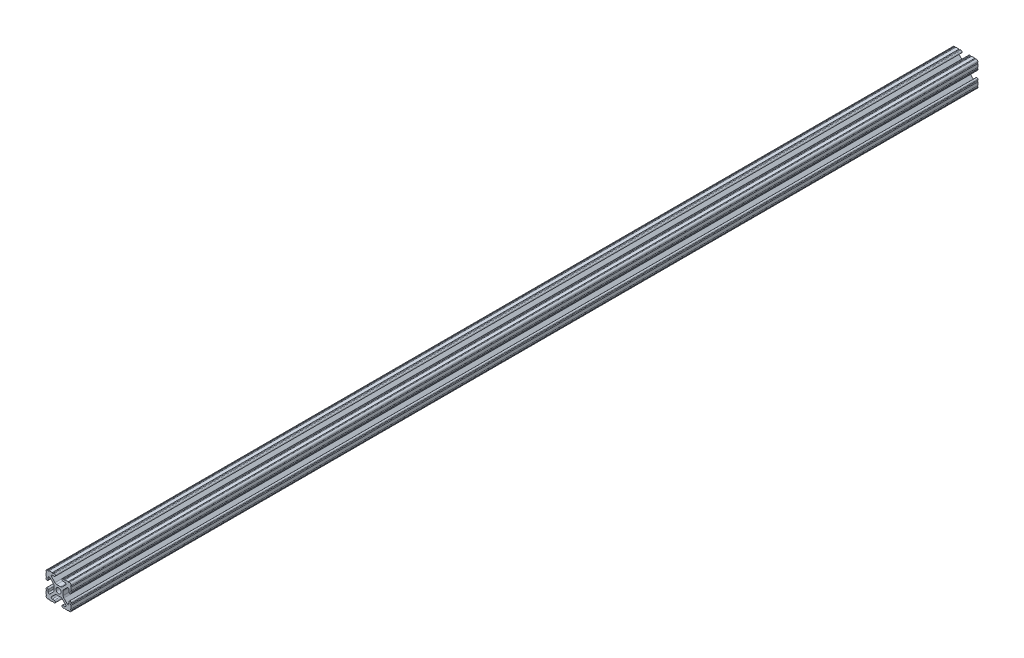
SolidWorks part; units mm, degrees
ref_plane "Front Plane" through (0, 0, 0) normal (0, 0, 1) x (1, 0, 0)
ref_plane "Top Plane" through (0, 0, 0) normal (0, 1, 0) x (1, 0, 0)
ref_plane "Right Plane" through (0, 0, 0) normal (1, 0, 0) x (0, 0, -1)
sketch "Sketch1" plane through (0, 0, 0) normal (0, 0, 1) x (1, 0, 0)
  line L0 (0, -12.7) -> (0, 12.7) construction
  line L1 (12.7, 0) -> (-12.7, 0) construction
  line L2 (3.2512, 12.7) -> (-3.2512, 12.7) construction
  line L3 (0, -4.5212) -> (0, 4.5212) construction
  line L4 (-3.2512, 12.7) -> (-3.2512, 10.4902) construction
  line L5 (12.7, -7.4168) -> (12.7, 7.4168) construction
  line L6 (0, -2.6035) -> (0, 2.6035) construction
  point P4 (0, 0)
  point P8 (0, 0)
  point P11 (0, 12.7)
  point P14 (0, 0)
  point P18 (12.7, 0)
  point P21 (0, 0)
sketch "Sketch2" plane through (0, 0, 0) normal (1, 0, 0) x (0, 0, -1)
  line L0 (-457.2, 0) -> (457.2, 0) construction
  point P4 (0, 0)
  dimension "Length" = 914.4
sketch "Sketch3" plane through (0, 0, 0) normal (0, 0, 1) x (1, 0, 0)
  line L1 (12.7, -12.7) -> (-12.7, -12.7)
  line L2 (12.7, -12.7) -> (12.7, 12.7)
  line L3 (12.7, 12.7) -> (-12.7, 12.7)
  line L4 (-12.7, -12.7) -> (-12.7, 12.7)
  line L5 (12.7, -12.7) -> (-12.7, 12.7) construction
  line L6 (12.7, 12.7) -> (-12.7, -12.7) construction
  point P0 (0, 0)
extrude "Boss-Extrude1" add sketch "Sketch3" along normal up to vertex (457.2 mm away) and the other way up to vertex (457.2 mm away) up to point (0, 0, 457.2) other way up to point (0, 0, -457.2)
sketch "Sketch4" plane through (0, 0, 457.2) normal (0, 0, 1) x (1, 0, 0)
  line L0 (-3.2512, 12.7) -> (-3.2512, 10.4902)
  line L1 (-3.2512, 10.4902) -> (-8.9276, 10.4902)
  line L2 (-8.9276, 10.4902) -> (-2.9586, 4.5212)
  line L3 (-2.9586, 4.5212) -> (2.9586, 4.5212)
  line L4 (0, -12.7) -> (0, 12.7) construction
  line L5 (12.7, 12.7) -> (-12.7, 12.7) construction
  line L6 (0, 12.7) -> (0, -12.7) construction
  line L7 (-12.7, 0) -> (12.7, 0) construction
  line L8 (-12.7, 12.7) -> (0, 0) construction
  line L9 (-12.7, 3.2512) -> (-10.4902, 3.2512)
  line L10 (-10.4902, 3.2512) -> (-10.4902, 8.9276)
  line L11 (-10.4902, 8.9276) -> (-4.5212, 2.9586)
  line L12 (-4.5212, 2.9586) -> (-4.5212, -2.9586)
  line L13 (4.5212, 2.9586) -> (4.5212, -2.9586)
  line L14 (10.4902, 8.9276) -> (4.5212, 2.9586)
  line L15 (10.4902, 3.2512) -> (10.4902, 8.9276)
  line L16 (12.7, 3.2512) -> (10.4902, 3.2512)
  line L17 (8.9276, 10.4902) -> (2.9586, 4.5212)
  line L18 (3.2512, 10.4902) -> (8.9276, 10.4902)
  line L19 (3.2512, 12.7) -> (3.2512, 10.4902)
  line L20 (3.2512, -12.7) -> (3.2512, -10.4902)
  line L21 (3.2512, -10.4902) -> (8.9276, -10.4902)
  line L22 (8.9276, -10.4902) -> (2.9586, -4.5212)
  line L23 (12.7, -3.2512) -> (10.4902, -3.2512)
  line L24 (10.4902, -3.2512) -> (10.4902, -8.9276)
  line L25 (10.4902, -8.9276) -> (4.5212, -2.9586)
  line L26 (-10.4902, -8.9276) -> (-4.5212, -2.9586)
  line L27 (-10.4902, -3.2512) -> (-10.4902, -8.9276)
  line L28 (-12.7, -3.2512) -> (-10.4902, -3.2512)
  line L29 (-2.9586, -4.5212) -> (2.9586, -4.5212)
  line L30 (-8.9276, -10.4902) -> (-2.9586, -4.5212)
  line L31 (-3.2512, -10.4902) -> (-8.9276, -10.4902)
  line L32 (-3.2512, -12.7) -> (-3.2512, -10.4902)
  line L33 (-12.7, 3.2512) -> (-12.7, -3.2512)
  line L34 (-3.2512, -12.7) -> (3.2512, -12.7)
  line L35 (12.7, -3.2512) -> (12.7, 3.2512)
  line L36 (3.2512, 12.7) -> (-3.2512, 12.7)
  line L37 (-12.7, 12.7) -> (-12.7, -12.7) construction
  line L38 (-12.7, -12.7) -> (12.7, -12.7) construction
  arc A3 (-6.3485, 10.4902) -> (-7.1039, 8.6665) centre (-6.3485, 9.4219) ccw
  arc A4 (7.1039, 8.6665) -> (6.3485, 10.4902) centre (6.3485, 9.4219) ccw
  arc A5 (8.6665, -7.1039) -> (10.4902, -6.3485) centre (9.4219, -6.3485) ccw
  arc A6 (10.4902, 6.3485) -> (8.6665, 7.1039) centre (9.4219, 6.3485) ccw
  arc A7 (-7.1039, -8.6665) -> (-6.3485, -10.4902) centre (-6.3485, -9.4219) ccw
  arc A8 (6.3485, -10.4902) -> (7.1039, -8.6665) centre (6.3485, -9.4219) ccw
  arc A9 (-8.6665, 7.1039) -> (-10.4902, 6.3485) centre (-9.4219, 6.3485) ccw
  arc A10 (-10.4902, -6.3485) -> (-8.6665, -7.1039) centre (-9.4219, -6.3485) ccw
  circle A11 centre (0, 0) radius 2.6035
  point P34 (0, 4.5212)
  point P45 (4.5212, 0)
  point P46 (-4.5212, 0)
  point P53 (0, -4.5212)
  point P81 (0, 0)
  line M2 (-12.7, 12.7) -> (-12.7, -12.7)
  line M3 (-12.7, -12.7) -> (12.7, -12.7)
  line M4 (12.7, -12.7) -> (12.7, 12.7)
  line M5 (12.7, 12.7) -> (-12.7, 12.7)
  dimension "D5" = 5.207
  dimension "D1" = 2.2098
  dimension "D2" = 2.2098
  dimension "D3" = 14.8336
  dimension "D4" = 4
extrude "Cut-Extrude1" cut sketch "Sketch4" against normal through all contours L17 A4 L18 L19 L0 L1 A3 L2 L3 M5 | L15 A6 L14 L13 L25 A5 L24 L23 L16 M4 | L21 A8 L22 L29 L30 A7 L31 L32 L20 M3 | L27 A10 L26 L12 L11 A9 L10 L9 L28 M2 | A11
sketch "Sketch5" plane through (0, 0, 457.2) normal (0, 0, 1) x (1, 0, 0)
  line L0 (-4.3561, 12.7) -> (-3.2512, 12.7)
  line L1 (-3.2512, 12.7) -> (-3.2512, 10.4902)
  line L2 (-3.2512, 10.4902) -> (-4.3561, 10.4902)
  line L3 (0, -12.7) -> (0, 12.7) construction
  line L4 (-3.2512, 12.7) -> (-12.7, 12.7) construction
  line L5 (3.2512, 10.4902) -> (4.3561, 10.4902)
  line L6 (3.2512, 12.7) -> (3.2512, 10.4902)
  line L7 (4.3561, 12.7) -> (3.2512, 12.7)
  line L8 (12.7, 4.3561) -> (12.7, 3.2512)
  line L9 (12.7, 3.2512) -> (10.4902, 3.2512)
  line L10 (10.4902, 3.2512) -> (10.4902, 4.3561)
  line L11 (10.4902, -3.2512) -> (10.4902, -4.3561)
  line L12 (12.7, -3.2512) -> (10.4902, -3.2512)
  line L13 (12.7, -4.3561) -> (12.7, -3.2512)
  line L14 (4.3561, -12.7) -> (3.2512, -12.7)
  line L15 (3.2512, -12.7) -> (3.2512, -10.4902)
  line L16 (3.2512, -10.4902) -> (4.3561, -10.4902)
  line L17 (-3.2512, -10.4902) -> (-4.3561, -10.4902)
  line L18 (-3.2512, -12.7) -> (-3.2512, -10.4902)
  line L19 (-4.3561, -12.7) -> (-3.2512, -12.7)
  line L20 (-12.7, -4.3561) -> (-12.7, -3.2512)
  line L21 (-12.7, -3.2512) -> (-10.4902, -3.2512)
  line L22 (-10.4902, -3.2512) -> (-10.4902, -4.3561)
  line L23 (-10.4902, 3.2512) -> (-10.4902, 4.3561)
  line L24 (-12.7, 3.2512) -> (-10.4902, 3.2512)
  line L25 (-12.7, 4.3561) -> (-12.7, 3.2512)
  line L26 (-12.7, 12.7) -> (-12.7, 3.2512) construction
  line L27 (-10.7124, 12.7) -> (-9.6075, 12.7)
  line L28 (-6.3436, 12.7) -> (-5.2387, 12.7)
  line L29 (-12.7, 10.7124) -> (-12.7, 9.6075)
  line L30 (-12.7, 6.3436) -> (-12.7, 5.2387)
  line L31 (6.3437, 12.7) -> (5.2388, 12.7)
  line L32 (10.7125, 12.7) -> (9.6076, 12.7)
  line L33 (12.7, 10.7125) -> (12.7, 9.6075)
  line L34 (12.7, 6.3436) -> (12.7, 5.2387)
  line L35 (12.7, -6.3437) -> (12.7, -5.2388)
  line L36 (12.7, -10.7125) -> (12.7, -9.6076)
  line L37 (10.7125, -12.7) -> (9.6076, -12.7)
  line L38 (6.3437, -12.7) -> (5.2388, -12.7)
  line L39 (-6.3436, -12.7) -> (-5.2387, -12.7)
  line L40 (-10.7124, -12.7) -> (-9.6075, -12.7)
  line L41 (-12.7, -10.7125) -> (-12.7, -9.6076)
  line L42 (-12.7, -6.3437) -> (-12.7, -5.2388)
  line L43 (12.7, 12.7) -> (3.2512, 12.7) construction
  line L44 (12.7, 3.2512) -> (12.7, 12.7) construction
  arc A0 (-4.3561, 10.4902) -> (-4.3561, 12.7) centre (-4.3561, 11.5951) ccw
  arc A1 (4.3561, 10.4902) -> (4.3561, 12.7) centre (4.3561, 11.5951) cw
  arc A2 (10.4902, 4.3561) -> (12.7, 4.3561) centre (11.5951, 4.3561) ccw
  arc A3 (10.4902, -4.3561) -> (12.7, -4.3561) centre (11.5951, -4.3561) cw
  arc A4 (4.3561, -10.4902) -> (4.3561, -12.7) centre (4.3561, -11.5951) ccw
  arc A5 (-4.3561, -10.4902) -> (-4.3561, -12.7) centre (-4.3561, -11.5951) cw
  arc A6 (-10.4902, -4.3561) -> (-12.7, -4.3561) centre (-11.5951, -4.3561) ccw
  arc A7 (-10.4902, 4.3561) -> (-12.7, 4.3561) centre (-11.5951, 4.3561) cw
  arc A8 (-10.7124, 12.7) -> (-9.6075, 12.7) centre (-10.16, 12.7) ccw
  arc A9 (-6.3436, 12.7) -> (-5.2387, 12.7) centre (-5.7912, 12.7) ccw
  arc A10 (-12.7, 9.6075) -> (-12.7, 10.7124) centre (-12.7, 10.16) ccw
  arc A11 (-12.7, 5.2387) -> (-12.7, 6.3436) centre (-12.7, 5.7912) ccw
  arc A12 (5.2388, 12.7) -> (6.3437, 12.7) centre (5.7912, 12.7) ccw
  arc A13 (9.6076, 12.7) -> (10.7125, 12.7) centre (10.16, 12.7) ccw
  arc A14 (12.7, 10.7125) -> (12.7, 9.6075) centre (12.7, 10.16) ccw
  arc A15 (12.7, 6.3436) -> (12.7, 5.2387) centre (12.7, 5.7912) ccw
  arc A16 (12.7, -5.2388) -> (12.7, -6.3437) centre (12.7, -5.7912) ccw
  arc A17 (12.7, -9.6076) -> (12.7, -10.7125) centre (12.7, -10.16) ccw
  arc A18 (10.7125, -12.7) -> (9.6076, -12.7) centre (10.16, -12.7) ccw
  arc A19 (6.3437, -12.7) -> (5.2388, -12.7) centre (5.7912, -12.7) ccw
  arc A20 (-5.2387, -12.7) -> (-6.3436, -12.7) centre (-5.7912, -12.7) ccw
  arc A21 (-9.6075, -12.7) -> (-10.7124, -12.7) centre (-10.16, -12.7) ccw
  arc A22 (-12.7, -10.7125) -> (-12.7, -9.6076) centre (-12.7, -10.16) ccw
  arc A23 (-12.7, -6.3437) -> (-12.7, -5.2388) centre (-12.7, -5.7912) ccw
  point P11 (0, 0)
  point P52 (0, 0)
  point P104 (0, 0)
  line M5 (3.2512, -10.4902) -> (3.2512, -12.7)
  line M6 (3.2512, -12.7) -> (12.7, -12.7)
  line M7 (12.7, -12.7) -> (12.7, -3.2512)
  line M8 (12.7, -3.2512) -> (10.4902, -3.2512)
  line M9 (10.4902, -3.2512) -> (10.4902, -6.3485)
  line M15 (10.4902, 6.3485) -> (10.4902, 3.2512)
  line M16 (10.4902, 3.2512) -> (12.7, 3.2512)
  line M17 (12.7, 3.2512) -> (12.7, 12.7)
  line M18 (12.7, 12.7) -> (3.2512, 12.7)
  line M19 (3.2512, 12.7) -> (3.2512, 10.4902)
  line M20 (3.2512, 10.4902) -> (6.3485, 10.4902)
  line M26 (-6.3485, 10.4902) -> (-3.2512, 10.4902)
  line M27 (-3.2512, 10.4902) -> (-3.2512, 12.7)
  line M28 (-3.2512, 12.7) -> (-12.7, 12.7)
  line M29 (-12.7, 12.7) -> (-12.7, 3.2512)
  line M30 (-12.7, 3.2512) -> (-10.4902, 3.2512)
  line M31 (-10.4902, 3.2512) -> (-10.4902, 6.3485)
  line M37 (-10.4902, -6.3485) -> (-10.4902, -3.2512)
  line M38 (-10.4902, -3.2512) -> (-12.7, -3.2512)
  line M39 (-12.7, -3.2512) -> (-12.7, -12.7)
  line M40 (-12.7, -12.7) -> (-3.2512, -12.7)
  line M41 (-3.2512, -12.7) -> (-3.2512, -10.4902)
  line M42 (-3.2512, -10.4902) -> (-6.3485, -10.4902)
  line M48 (6.3485, -10.4902) -> (3.2512, -10.4902)
  dimension "D2" = 0.5524
  dimension "D3" = 2.54
  dimension "D4" = 2.54
  dimension "D5" = 2.54
  dimension "D6" = 2.54
  dimension "D1" = 4
  dimension "D7" = 4
extrude "Cut-Extrude2" cut sketch "Sketch5" against normal through all contours A7 M30 M29 | A7 L24 M31 | A6 L21 M39 | A6 M37 M38 | A5 L18 M42 | A5 M41 M40 | A4 M48 M5 | A4 L15 M6 | A3 L12 M9 | A3 M8 M7 | A2 M15 M16 | A2 L9 M17 | A1 M19 M18 | A1 L6 M20 | A0 L1 M28 | A0 M26 M27 | A11 L30 | A10 L29 | A8 L27 | A9 L28 | L31 A12 | L32 A13 | L33 A14 | L34 A15 | L42 A23 | L41 A22 | L40 A21 | L39 A20 | L36 A17 | L35 A16 | L37 A18 | L38 A19
fillet "Fillet1" radius 2.54 8 edges at (2.9586, -4.5212, 0) (-2.9586, -4.5212, 0) (4.5212, -2.9586, 0) (4.5212, 2.9586, 0) (-2.9586, 4.5212, 0) (2.9586, 4.5212, 0) (-4.5212, -2.9586, 0) (-4.5212, 2.9586, 0)
fillet "Fillet2" radius 1.778 4 edges at (12.7, -12.7, 0) (12.7, 12.7, 0) (-12.7, -12.7, 0) (-12.7, 12.7, 0)
equation "\"D2@Sketch4\"=\"Thickness@Sketch1\""
equation "\"D1@Sketch4\"=\"Thickness@Sketch1\""
equation "\"D3@Sketch4\"=\"Opening Width@Sketch1\""
equation "\"D5@Sketch4\"=\"Hole Dia@Sketch1\""
equation "\"D2@Sketch5\"=\"Thickness@Sketch1\"/4"
equation "\"D3@Sketch5\"=\"Height@Sketch1\"/10"
equation "\"D4@Sketch5\"=\"D3@Sketch5\""
equation "\"D5@Sketch5\"=\"D4@Sketch5\""
equation "\"D6@Sketch5\"=\"D5@Sketch5\""
